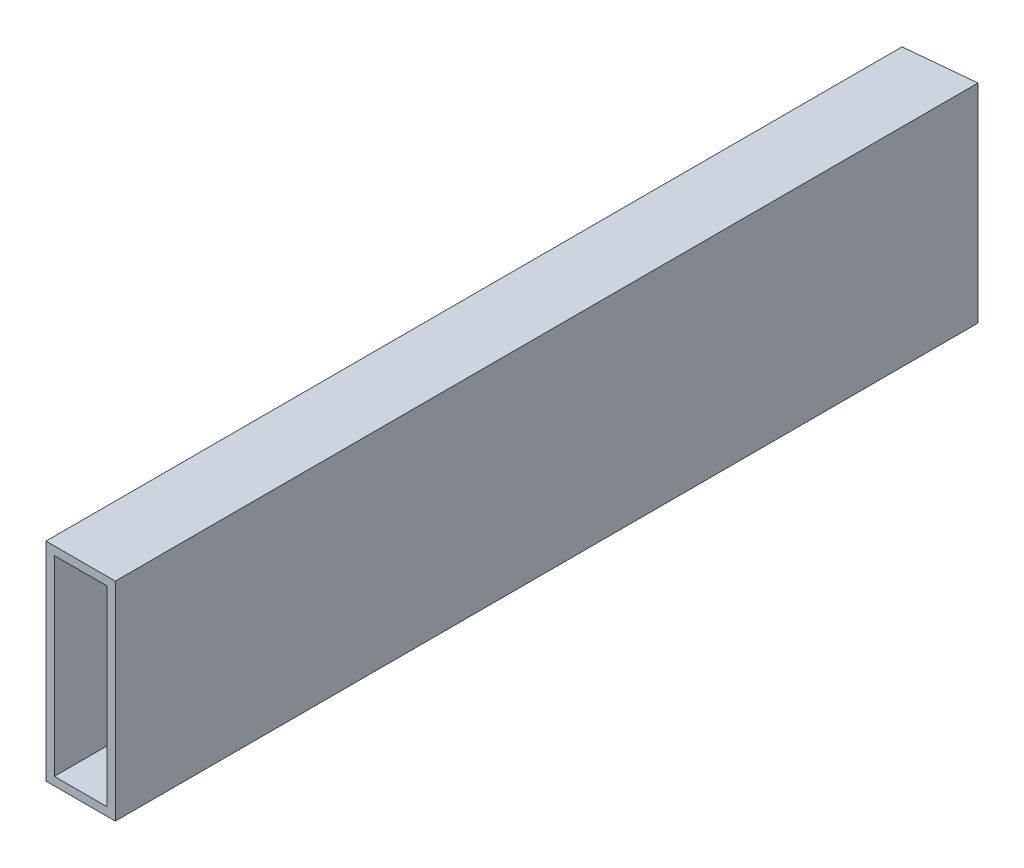
SolidWorks part; units mm, degrees
material "A500"
ref_plane "Front Plane" through (0, 0, 0) normal (0, 0, 1) x (1, 0, 0)
ref_plane "Top Plane" through (0, 0, 0) normal (0, 1, 0) x (1, 0, 0)
ref_plane "Right Plane" through (0, 0, 0) normal (1, 0, 0) x (0, 0, -1)
sketch "Sketch2" plane through (0, 0, 0) normal (0, 0, 1) x (1, 0, 0)
  line L0 (0, 0) -> (0, 38.1)
  line L1 (0, 38.1) -> (12.7, 38.1)
  line L2 (12.7, 38.1) -> (12.7, 0)
  line L3 (12.7, 0) -> (0, 0)
  line L4 (12.7, -38.1) -> (12.7, -35.052)
  line L5 (0, 0) -> (-12.7, 0)
  line L6 (0, 0) -> (0, -38.1)
  line L7 (0, -38.1) -> (-12.7, -38.1)
  line L8 (-12.7, 0) -> (-12.7, -38.1)
  line L9 (-12.7, -38.1) -> (12.7, -38.1)
  line L10 (-12.7, -38.1) -> (-12.7, 38.1)
  line L11 (-12.7, 38.1) -> (12.7, 38.1)
  line L12 (12.7, -38.1) -> (12.7, 38.1)
  line L13 (12.7, -35.052) -> (9.652, -35.052)
  line L14 (-12.7, 38.1) -> (-9.652, 38.1)
  line L15 (-9.652, 38.1) -> (-9.652, 35.052)
  line L17 (-9.652, 35.052) -> (9.652, 35.052)
  line L18 (-9.652, 35.052) -> (-9.652, -35.052)
  line L19 (-9.652, -35.052) -> (9.652, -35.052)
  line L20 (9.652, 35.052) -> (9.652, -35.052)
  dimension "D1" = 38.1
  dimension "D2" = 12.7
  dimension "D3" = 38.1
  dimension "D4" = 12.7
  dimension "D5" = 3.048
  dimension "D6" = 3.048
  dimension "D7" = 3.048
  dimension "D8" = 3.048
extrude "Boss-Extrude1" add sketch "Sketch2" along normal up to vertex (315 mm away) contours L18 L15 L11 L10 L5 | L15 L17 L0 L11 | L17 L20 L3 L2 L1 L0 | L3 L20 L13 L12 | L19 L18 L5 L8 L7 L6 | L19 L6 L9 L4 L13
sketch "Sketch3" plane through (0, 0, 0) normal (0, 0, -1) x (-1, 0, 0)
  line L1 (-12.7, 38.1) -> (12.7, 38.1)
  line L2 (-12.7, 38.1) -> (-12.7, -38.1)
  line L3 (-12.7, -38.1) -> (12.7, -38.1)
  line L4 (12.7, 38.1) -> (12.7, -38.1)
  line L5 (-9.652, 35.052) -> (9.652, 35.052)
  line L6 (-9.652, 35.052) -> (-9.652, -35.052)
  line L7 (-9.652, -35.052) -> (9.652, -35.052)
  line L8 (9.652, 35.052) -> (9.652, -35.052)
extrude "Boss-Extrude2" add sketch "Sketch3" along normal blind 50
sketch "Sketch4" plane through (0, 38.1, 0) normal (0, 1, 0) x (1, 0, 0)
  line L0 (-70.9498, -6.8033) -> (70.9498, 6.8033)
  line L1 (0, -50) -> (0, 0)
  line L2 (0, -315) -> (0, 0) construction
  line L3 (0, 0) -> (-9.5015, 49.0889)
  line L4 (0, 0) -> (-14.8, 76.4631) construction
  line L5 (-9.5015, 49.0889) -> (-70.9498, -6.8033)
  line L6 (0, -50) -> (-70.9498, -6.8033)
  line L7 (-70.9498, -6.8033) -> (70.9498, 6.8033)
  line L8 (-70.9498, -6.8033) -> (-77.5602, 62.1347)
  line L9 (70.9498, 6.8033) -> (64.3394, 75.7413)
  line L10 (-77.5602, 62.1347) -> (64.3394, 75.7413)
  line M6 (12.7, -315) -> (12.7, 50)
  line M7 (12.7, 50) -> (-12.7, 50)
  line M8 (-12.7, 50) -> (-12.7, -315)
  dimension "D1" = 50
  dimension "D2" = 50
extrude "Cut-Extrude1" cut sketch "Sketch4" against normal through all both and the other way through all contours L5 L0 M8 | L10 L8 L5 L0 L9 M8 M7 M6 | L3 L5 L0 M8 | L5 L3 L0 M6 M7 M8
equation "\"D3@Sketch2\"=\"D1@Sketch2\""
equation "\"D4@Sketch2\"=\"D2@Sketch2\""
